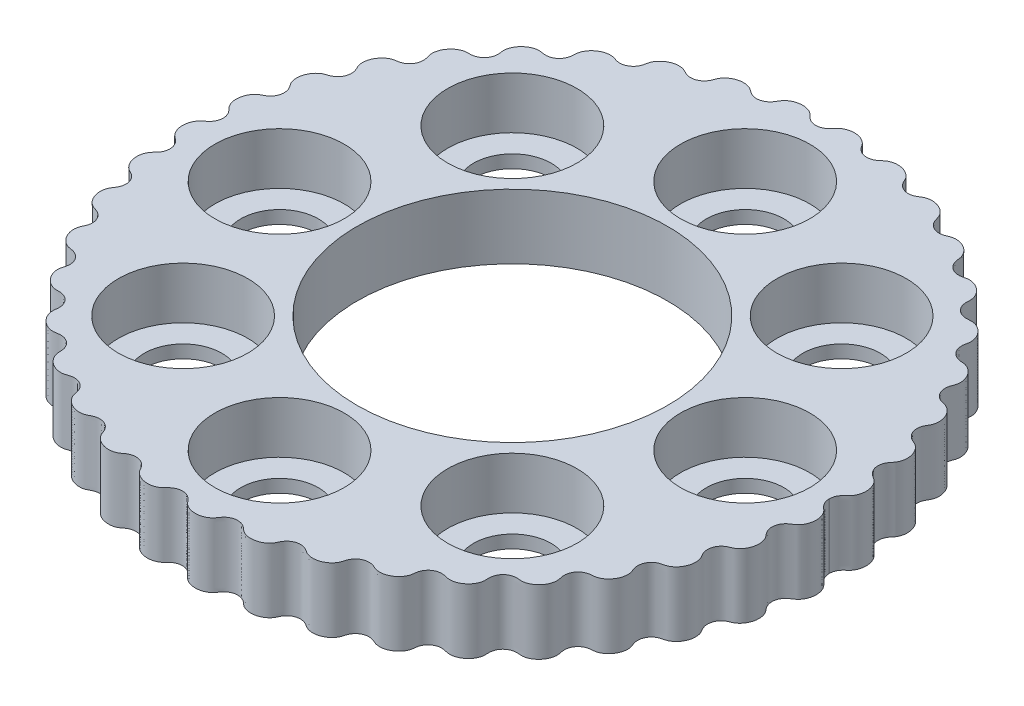
SolidWorks part; units mm, degrees
material "Plastic-FDM-PLA-pro"
ref_plane "Front Plane" through (0, 0, 0) normal (0, 0, 1) x (1, 0, 0)
ref_plane "Top Plane" through (0, 0, 0) normal (0, 1, 0) x (1, 0, 0)
ref_plane "Right Plane" through (0, 0, 0) normal (1, 0, 0) x (0, 0, -1)
sketch "Sketch1" plane through (0, 0, 0) normal (0, 1, 0) x (1, 0, 0)
  spline S0 degree 4 poles (21.6064, 11.6128) (21.6414, 11.4763) (21.7469, 11.2449) (21.9844, 10.9896) (22.3715, 10.8276) (22.6869, 10.7857) (22.9052, 10.6672) (23.101, 10.52) (23.2912, 10.3173) (23.4718, 10.0222) (23.5794, 9.667) (23.5943, 9.3186) (23.5416, 9.0412) (23.4555, 8.8423) (23.3486, 8.6778) (23.2672, 8.5195) (23.2069, 8.3378) (23.1769, 8.1351) (23.1918, 7.8658) (23.2852, 7.5991) (23.447, 7.374) (23.6777, 7.1845) (23.8829, 7.0851) (24.0858, 7.0142) (24.2547, 6.9048) (24.3764, 6.799) (24.5108, 6.6487) (24.6611, 6.4154) (24.7857, 6.0883) (24.8278, 5.7024) (24.7657, 5.333) (24.6291, 5.0248) (24.4255, 4.8149) (24.2352, 4.5318) (24.1366, 4.1601) (24.1814, 3.7967) (24.3419, 3.4935) (24.5162, 3.3067) (24.6648, 3.1936) (24.8483, 3.087) (25.0116, 2.971) (25.142, 2.817) (25.2689, 2.6137) (25.3735, 2.3636) (25.4403, 2.0313) (25.4214, 1.6748) (25.3264, 1.3624) (25.2002, 1.1354) (25.0791, 0.9924) (24.9144, 0.8484) (24.7545, 0.7145) (24.6219, 0.5035) (24.5339, 0.3154) (24.4987, 0.0763) (24.4972, -0.0467) (24.5201, -0.2316) (24.5633, -0.371) (24.6305, -0.5179) (24.7235, -0.6591) (24.8424, -0.7928) (24.9875, -0.9088) (25.1511, -1.0633) (25.293, -1.2851) (25.4049, -1.5905) (25.4424, -1.9737) (25.3882, -2.3415) (25.2499, -2.6627) (25.0662, -2.9239) (24.8433, -3.0978) (24.5517, -3.2517) (24.2918, -3.541) (24.1569, -3.8872) (24.16, -4.2453) (24.2535, -4.5391) (24.3852, -4.772) (24.6388, -5.0192) (24.7975, -5.3974) (24.8306, -5.8363) (24.735, -6.2498) (24.582, -6.5585) (24.3902, -6.792) (24.1849, -6.9706) (23.9409, -7.0651) (23.7071, -7.1659) (23.5087, -7.3191) (23.3504, -7.5023) (23.2169, -7.7647) (23.1632, -8.0717) (23.2057, -8.3939) (23.3413, -8.6751) (23.491, -8.8942) (23.5762, -9.1776) (23.5983, -9.4998) (23.5348, -9.8472) (23.3798, -10.1906) (23.1789, -10.451) (22.9676, -10.6305) (22.7649, -10.7428) (22.5892, -10.7977) (22.3868, -10.8377) (22.1901, -10.9044) (21.9966, -11.0169) (21.7651, -11.2346) (21.5956, -11.5351) (21.5394, -11.9062) (21.6321, -12.2847) (21.7646, -12.5496) (21.7896, -12.787) (21.7821, -13.0234) (21.7272, -13.2891) (21.5951, -13.6002) (21.3432, -13.9284) (21.0152, -14.1682) (20.6947, -14.2804) (20.4313, -14.2827) (20.2219, -14.3105) (20.0313, -14.3657) (19.7839, -14.4936) (19.5202, -14.7509) (19.3691, -15.1052) (19.358, -15.5014) (19.4626, -15.8335) (19.4645, -16.1376) (19.3797, -16.4671) (19.2041, -16.7975) (18.9497, -17.076) (18.6389, -17.2749) (18.3217, -17.3893) (18.0234, -17.406) (17.6885, -17.3481) (17.2876, -17.4221) (16.9111, -17.6604) (16.701, -18.015) (16.6406, -18.3304) (16.6445, -18.5921) (16.6666, -18.826) (16.6068, -19.103) (16.4483, -19.4313) (16.1768, -19.7449) (15.8266, -19.9759) (15.4618, -20.0854) (15.1639, -20.0942) (14.952, -20.0498) (14.7885, -20.002) (14.6205, -19.9753) (14.4515, -19.9734) (14.1835, -20.0112) (13.9066, -20.1364) (13.6633, -20.3656) (13.5183, -20.6583) (13.4634, -20.8736) (13.4458, -21.0651) (13.4259, -21.2273) (13.3666, -21.4185) (13.2572, -21.6273) (13.0672, -21.8645) (12.7739, -22.0937) (12.4479, -22.2382) (12.1139, -22.2969) (11.8439, -22.2832) (11.6455, -22.2339) (11.4786, -22.1566) (11.3266, -22.0917) (11.1442, -22.0428) (10.9328, -22.0228) (10.6452, -22.0575) (10.3631, -22.1865) (10.1408, -22.39) (9.9781, -22.6552) (9.9083, -22.8739) (9.8608, -23.0787) (9.7525, -23.2945) (9.5985, -23.4966) (9.3551, -23.7042) (9.0121, -23.8756) (8.6687, -23.9514) (8.3512, -23.9469) (8.1058, -23.89) (7.9336, -23.8157) (7.7931, -23.7235) (7.6679, -23.6413) (7.5165, -23.5662) (7.3372, -23.508) (7.0515, -23.4713) (6.6931, -23.5377) (6.3655, -23.7489) (6.1584, -24.0486) (6.0643, -24.2923) (5.9427, -24.495) (5.7771, -24.6722) (5.5202, -24.8548) (5.1577, -24.9945) (4.7865, -25.0373) (4.4327, -24.988) (4.1695, -24.8845) (3.9951, -24.7688) (3.8656, -24.6453) (3.7525, -24.5466) (3.6093, -24.4489) (3.4314, -24.3647) (3.1621, -24.2973) (2.8589, -24.3139) (2.5753, -24.4209) (2.3558, -24.59) (2.2246, -24.737) (2.1274, -24.882) (2.043, -25.0091) (1.9052, -25.1589) (1.6988, -25.3081) (1.3977, -25.4399) (1.0011, -25.503) (0.6294, -25.4653) (0.3077, -25.3467) (0.0836, -25.1987) (-0.0532, -25.0604) (-0.1778, -24.8926) (-0.3225, -24.7352) (-0.5188, -24.5957) (-0.7661, -24.4996) (-1.0146, -24.4675) (-1.2631, -24.4929) (-1.4934, -24.5761) (-1.7123, -24.7098) (-1.8904, -24.9013) (-2.0764, -25.0987) (-2.3287, -25.228) (-2.6322, -25.321) (-2.9953, -25.3415) (-3.3913, -25.2694) (-3.7257, -25.0998) (-3.9503, -24.901) (-4.079, -24.7143) (-4.1499, -24.578) (-4.2687, -24.3844) (-4.4849, -24.1551) (-4.8019, -23.9927) (-5.1889, -23.9616) (-5.4906, -24.0414) (-5.6943, -24.1469) (-5.8507, -24.2667) (-5.9811, -24.3697) (-6.1604, -24.4671) (-6.3907, -24.539) (-6.6975, -24.5713) (-7.0706, -24.5216) (-7.4033, -24.3887) (-7.679, -24.1911) (-7.8581, -23.9886) (-7.9629, -23.8127) (-8.0239, -23.6389) (-8.0813, -23.4835) (-8.1705, -23.3175) (-8.2998, -23.1506) (-8.5196, -22.9657) (-8.8045, -22.8475) (-9.1054, -22.8225) (-9.4112, -22.8846) (-9.6211, -22.9835) (-9.8015, -23.0932) (-10.0314, -23.1678) (-10.2833, -23.1991) (-10.6025, -23.1704) (-10.9638, -23.0446) (-11.2595, -22.8521) (-11.4763, -22.6216) (-11.6301, -22.3749) (-11.7084, -22.1238) (-11.7363, -21.8619) (-11.8445, -21.6178) (-12.0322, -21.3534) (-12.3288, -21.1371) (-12.7054, -21.043) (-13.067, -21.0972) (-13.3074, -21.197) (-13.5367, -21.2529) (-13.7784, -21.2587) (-14.0861, -21.2036) (-14.432, -21.0455) (-14.7219, -20.8162) (-14.9308, -20.5358) (-15.0653, -20.2461) (-15.1044, -19.966) (-15.092, -19.6366) (-15.2124, -19.2669) (-15.4448, -18.9769) (-15.7565, -18.8005) (-16.0577, -18.7346) (-16.3252, -18.7322) (-16.6661, -18.8282) (-17.073, -18.7766) (-17.4696, -18.5859) (-17.78, -18.2963) (-17.9708, -18.0094) (-18.0771, -17.7266) (-18.1291, -17.4595) (-18.089, -17.2009) (-18.0594, -16.9481) (-18.0928, -16.6996) (-18.1723, -16.471) (-18.3328, -16.2242) (-18.5719, -16.0241) (-18.8721, -15.8998) (-19.1835, -15.8766) (-19.4481, -15.8967) (-19.7361, -15.8288) (-20.0262, -15.6869) (-20.2953, -15.4582) (-20.5152, -15.1523) (-20.6403, -14.8481) (-20.6901, -14.5753) (-20.6859, -14.3436) (-20.6457, -14.164) (-20.5792, -13.9687) (-20.5386, -13.765) (-20.5392, -13.5412) (-20.612, -13.2319) (-20.7875, -12.9349) (-21.0807, -12.7006) (-21.4549, -12.5916) (-21.7505, -12.5739) (-21.9686, -12.4769) (-22.1696, -12.3522) (-22.3723, -12.1718) (-22.5756, -11.9018) (-22.7339, -11.5196) (-22.7776, -11.1156) (-22.7145, -10.782) (-22.5849, -10.5527) (-22.5042, -10.3575) (-22.4568, -10.1648) (-22.4437, -9.8866) (-22.5347, -9.5296) (-22.7659, -9.2216) (-23.1036, -9.0138) (-23.4433, -8.9385) (-23.708, -8.7878) (-23.9503, -8.5501) (-24.15, -8.2319) (-24.2617, -7.874) (-24.2819, -7.5029) (-24.2248, -7.2115) (-24.1394, -7.0047) (-24.0111, -6.8223) (-23.8576, -6.6068) (-23.7298, -6.2619) (-23.7513, -5.8143) (-23.9511, -5.4566) (-24.1952, -5.2457) (-24.4233, -5.1187) (-24.6372, -5.0206) (-24.847, -4.8305) (-25.0522, -4.5291) (-25.1879, -4.1371) (-25.213, -3.7183) (-25.1254, -3.3477) (-24.9841, -3.0853) (-24.8398, -2.924) (-24.7165, -2.8063) (-24.583, -2.6414) (-24.4354, -2.3636) (-24.3819, -2.0177) (-24.4687, -1.6501) (-24.6496, -1.3782) (-24.8086, -1.2229) (-24.9657, -1.1119) (-25.0962, -1.0135) (-25.2322, -0.8667) (-25.3584, -0.6675) (-25.4688, -0.3843) (-25.5206, -0.0157) (-25.4828, 0.3389) (-25.3667, 0.6575) (-25.2198, 0.8845) (-25.0779, 1.0317) (-24.9276, 1.1375) (-24.7953, 1.2367) (-24.6618, 1.3702) (-24.5388, 1.5433) (-24.4249, 1.8097) (-24.3956, 2.1184) (-24.4607, 2.4128) (-24.609, 2.6862) (-24.7635, 2.8561) (-24.9171, 2.9996) (-25.0499, 3.2013) (-25.1479, 3.4357) (-25.206, 3.7503) (-25.183, 4.133) (-25.0769, 4.4684) (-24.9143, 4.7411) (-24.7423, 4.9251) (-24.5919, 5.0371) (-24.4417, 5.1126) (-24.308, 5.18) (-24.1672, 5.2736) (-24.0272, 5.3998) (-23.8525, 5.6288) (-23.7308, 5.9724) (-23.7499, 6.3618) (-23.9059, 6.691) (-24.0699, 6.8943) (-24.1846, 7.1009) (-24.2553, 7.333) (-24.285, 7.6467) (-24.2247, 8.0305) (-24.0763, 8.3734) (-23.8566, 8.6551) (-23.6354, 8.8313) (-23.448, 8.9246) (-23.2763, 8.9749) (-23.1342, 9.0235) (-22.9781, 9.0987) (-22.8162, 9.2106) (-22.6231, 9.4101) (-22.486, 9.681) (-22.4368, 9.9801) (-22.4734, 10.2548) (-22.5351, 10.4418) (-22.6121, 10.5986) (-22.68, 10.7352) (-22.7408, 10.9295) (-22.7669, 11.1828) (-22.7304, 11.5095) (-22.5868, 11.8844) (-22.3683, 12.1876) (-22.1047, 12.4069) (-21.8645, 12.5269) (-21.6764, 12.5763) (-21.4687, 12.6003) (-21.2601, 12.6468) (-21.0411, 12.7471) (-20.8343, 12.9132) (-20.6822, 13.1123) (-20.5799, 13.3403) (-20.5369, 13.5813) (-20.5431, 13.8377) (-20.6199, 14.0877) (-20.6979, 14.3475) (-20.6838, 14.6306) (-20.6125, 14.94) (-20.4488, 15.2647) (-20.1883, 15.5716) (-19.8743, 15.7764) (-19.5899, 15.8715) (-19.3639, 15.8897) (-19.2104, 15.883) (-18.9834, 15.889) (-18.6767, 15.9615) (-18.3775, 16.1547) (-18.157, 16.4743) (-18.0752, 16.7755) (-18.0647, 17.0047) (-18.0902, 17.2001) (-18.1143, 17.3645) (-18.1089, 17.5685) (-18.0561, 17.8039) (-17.9307, 18.0858) (-17.7011, 18.3841) (-17.4196, 18.6058) (-17.1106, 18.7458) (-16.8457, 18.7996) (-16.641, 18.8024) (-16.46, 18.7684) (-16.2967, 18.7403) (-16.1084, 18.7346) (-15.8992, 18.7631) (-15.6291, 18.861) (-15.3843, 19.0486) (-15.2122, 19.2966) (-15.113, 19.5925) (-15.0937, 19.8238) (-15.0986, 20.035) (-15.0482, 20.2713) (-14.9494, 20.5052) (-14.765, 20.7672) (-14.4753, 21.0172) (-14.1608, 21.177) (-13.8528, 21.2496) (-13.5622, 21.2594) (-13.3057, 21.2017) (-13.0648, 21.0949) (-12.7994, 21.0666) (-12.4765, 21.0969) (-12.1409, 21.2456) (-11.8711, 21.5246) (-11.7372, 21.8649) (-11.7034, 22.123) (-11.6373, 22.3495) (-11.5214, 22.5617) (-11.3198, 22.8007) (-11.01, 23.0212) (-10.6664, 23.1577) (-10.3191, 23.1983) (-10.0011, 23.17) (-9.7389, 23.0639) (-9.4598, 22.8883) (-9.0794, 22.8078) (-8.7121, 22.864) (-8.4035, 23.0457) (-8.1958, 23.2737) (-8.06, 23.5041) (-7.9727, 23.8474) (-7.7246, 24.1739) (-7.3611, 24.4221) (-6.9551, 24.546) (-6.6113, 24.5678) (-6.3132, 24.5186) (-6.0559, 24.4301) (-5.8519, 24.266) (-5.6478, 24.114) (-5.4159, 24.0187) (-5.1781, 23.9732) (-4.8842, 23.9888) (-4.5914, 24.0957) (-4.3336, 24.2935) (-4.1578, 24.5516) (-4.043, 24.7909) (-3.8401, 25.0063) (-3.5722, 25.1866) (-3.2396, 25.3053) (-2.8647, 25.3428) (-2.5387, 25.299) (-2.2776, 25.2058) (-2.079, 25.0864) (-1.9435, 24.9618) (-1.8077, 24.8065) (-1.6516, 24.6695) (-1.4575, 24.5581) (-1.1533, 24.4665) (-0.8082, 24.4699) (-0.4587, 24.6067) (-0.1772, 24.8762) (-0.0141, 25.1234) (0.179, 25.2638) (0.3874, 25.3755) (0.645, 25.4608) (0.9805, 25.502) (1.3907, 25.448) (1.7624, 25.2838) (2.0197, 25.0624) (2.1535, 24.8355) (2.2823, 24.668) (2.4253, 24.5306) (2.6597, 24.3802) (3.0144, 24.2805) (3.3968, 24.3266) (3.7456, 24.5152) (3.9807, 24.7717) (4.2435, 24.9256) (4.5705, 25.0166) (4.9458, 25.0305) (5.3119, 24.9483) (5.643, 24.7801) (5.8673, 24.5852) (6.0028, 24.4076) (6.0826, 24.2396) (6.143, 24.1028) (6.2565, 23.9062) (6.4759, 23.6637) (6.8407, 23.4765) (7.2497, 23.4705) (7.5547, 23.5765) (7.7786, 23.7105) (7.9706, 23.8467) (8.2401, 23.9334) (8.6038, 23.9604) (9.011, 23.882) (9.3863, 23.6943) (9.6634, 23.4332) (9.82, 23.1796) (9.8876, 22.974) (9.9279, 22.8084) (10.0039, 22.6103) (10.1706, 22.3437) (10.4434, 22.1243) (10.8051, 22.0156) (11.1311, 22.0362) (11.3451, 22.0963) (11.5198, 22.1769) (11.6703, 22.2407) (11.8654, 22.285) (12.101, 22.2948) (12.4015, 22.2488) (12.7467, 22.1094) (13.0348, 21.8994) (13.2527, 21.6395) (13.3758, 21.3988) (13.4324, 21.2023) (13.4489, 21.0192) (13.4686, 20.855) (13.5175, 20.6726) (13.6059, 20.4796) (13.7797, 20.2478) (14.0324, 20.068) (14.3198, 19.9772) (14.6308, 19.9689) (14.8552, 20.0177) (15.0562, 20.079) (15.2973, 20.0932) (15.5493, 20.0609) (15.8508, 19.9539) (16.1707, 19.7426) (16.4081, 19.4831) (16.563, 19.2059) (16.6364, 18.9649) (16.6582, 18.7787) (16.6486, 18.6109) (16.64, 18.4614) (16.6507, 18.2926) (16.6899, 18.1083) (16.8009, 17.8425) (17.0376, 17.5653) (17.3843, 17.3871) (17.7475, 17.3576) (18.0055, 17.398) (18.2418, 17.394) (18.4781, 17.3393) (18.7647, 17.2081) (19.0669, 16.964) (19.2897, 16.664) (19.4239, 16.3329) (19.4658, 16.0532) (19.4529, 15.8443) (19.4107, 15.6704) (19.3817, 15.5231) (19.3687, 15.3503) (19.3847, 15.1541) (19.4609, 14.8872) (19.6269, 14.633) (19.8614, 14.4408) (20.1176, 14.3352) (20.3104, 14.2951) (20.4846, 14.2834) (20.6369, 14.2739) (20.8355, 14.2294) (21.068, 14.1253) (21.3326, 13.9304) (21.5856, 13.6186) (21.7389, 13.2778) (21.797, 12.9399) (21.7809, 12.6717) (21.7296, 12.4842) (21.6466, 12.2922) (21.5826, 12.0887) (21.5598, 11.8481) (21.6099, 11.5263) (21.753, 11.2421) (21.9754, 11.0236) (22.2554, 10.8726) (22.5102, 10.8132) (22.7742, 10.7514) (23.0124, 10.5973) (23.2447, 10.3811) (23.444, 10.0768) (23.5796, 9.6979) (23.5999, 9.3235) (23.5401, 9.0297) (23.4429, 8.8249) (23.3603, 8.6953) (23.252, 8.4958) (23.1614, 8.1939) (23.1791, 7.8382) (23.3456, 7.4874) (23.5655, 7.2659) (23.7587, 7.1422) (23.9407, 7.0666) (24.0951, 7.0052) (24.2692, 6.8986) (24.4466, 6.7352) (24.6287, 6.4847) (24.7728, 6.1345) (24.8235, 5.7774) (24.7881, 5.4376) (24.7001, 5.1799) (24.5973, 5.0011) (24.4749, 4.8604) (24.3681, 4.7299) (24.27, 4.5656) (24.1928, 4.366) (24.1487, 4.0806) (24.1956, 3.7768) (24.3283, 3.5111) (24.5371, 3.2801) (24.7311, 3.1513) (24.9205, 3.0449) (25.0679, 2.9033) (25.172, 2.7726) (25.2819, 2.5886) (25.3847, 2.3274) (25.4421, 1.9891) (25.4127, 1.6245) (25.3025, 1.3024) (25.1554, 1.0688) (25.0038, 0.9249) (24.8611, 0.8033) (24.7491, 0.6995) (24.6413, 0.5276) (24.5505, 0.3764) (24.4955, 0.0867) (24.4947, -0.0797) (24.5547, -0.3974) (24.6786, -0.5985) (24.8655, -0.8322) (25.1022, -0.9903) (25.2927, -1.2763) (25.4173, -1.6256) (25.4428, -2.0161) (25.3682, -2.397) (25.2352, -2.6864) (25.0928, -2.88) (24.9184, -3.0461) (24.7326, -3.1512) (24.5436, -3.2751) (24.3796, -3.4542) (24.2658, -3.6365) (24.168, -3.906) (24.1508, -4.2123) (24.2348, -4.5312) (24.4248, -4.814) (24.6285, -5.0241) (24.7655, -5.332) (24.8277, -5.7016) (24.786, -6.0872) (24.6469, -6.4527) (24.4651, -6.7144) (24.2897, -6.8818) (24.0868, -7.0138) (23.8842, -7.0847) (23.6788, -7.1838) (23.448, -7.3729) (23.2859, -7.5977) (23.1922, -7.8642) (23.1769, -8.1335) (23.2066, -8.3362) (23.2665, -8.518) (23.3478, -8.6765) (23.4547, -8.8409) (23.5411, -9.0397) (23.5942, -9.3169) (23.5797, -9.6657) (23.4731, -10.0182) (23.274, -10.3468) (23.052, -10.568) (22.8501, -10.7012) (22.6276, -10.7926) (22.4169, -10.8278) (22.2005, -10.8982) (21.9459, -11.0512) (21.7636, -11.2408) (21.6636, -11.4244) (21.6175, -11.5694) (21.6065, -11.6122) knots 0 0 0 0 0 0.002654 0.004786 0.006316 0.007845 0.008629 0.009413 0.01098 0.013063 0.015147 0.016343 0.017539 0.018381 0.019222 0.020064 0.020905 0.021995 0.023085 0.025147 0.026164 0.027182 0.028699 0.029457 0.030216 0.030982 0.031748 0.033281 0.035433 0.037585 0.038965 0.040346 0.041714 0.043082 0.0454 0.04745 0.048461 0.049472 0.050225 0.050979 0.052487 0.053248 0.054009 0.055531 0.057585 0.059638 0.060666 0.061695 0.062456 0.063216 0.064738 0.065778 0.066818 0.067667 0.068385 0.069102 0.06982 0.070538 0.071421 0.072304 0.073187 0.07407 0.075664 0.077258 0.079288 0.081318 0.082594 0.083869 0.085257 0.086645 0.088819 0.091044 0.092148 0.093252 0.094656 0.096059 0.098784 0.100818 0.102852 0.104037 0.105222 0.106567 0.107911 0.108976 0.110041 0.111265 0.11249 0.114477 0.115881 0.117284 0.118381 0.119479 0.121426 0.123373 0.124976 0.126579 0.127595 0.12861 0.129335 0.13006 0.131509 0.132527 0.133545 0.136038 0.137928 0.13939 0.140852 0.141613 0.142374 0.143896 0.145943 0.147989 0.150092 0.151522 0.152237 0.152953 0.154104 0.155255 0.157496 0.159774 0.16119 0.162605 0.16404 0.165474 0.167569 0.169664 0.171057 0.172449 0.173868 0.175287 0.177453 0.179996 0.182057 0.182779 0.183501 0.184946 0.186499 0.188052 0.190377 0.192702 0.194343 0.195163 0.195983 0.196782 0.19758 0.198378 0.199176 0.201896 0.203215 0.204534 0.205309 0.206084 0.206859 0.207634 0.209084 0.210533 0.21258 0.214627 0.215764 0.216902 0.217685 0.218468 0.219251 0.220035 0.221253 0.222471 0.224698 0.225787 0.226877 0.228317 0.229037 0.229758 0.231433 0.233109 0.235038 0.236967 0.238024 0.239082 0.239792 0.240502 0.241211 0.241921 0.242991 0.24406 0.246641 0.248667 0.250125 0.250854 0.251582 0.253135 0.254688 0.25678 0.258872 0.260133 0.261393 0.262104 0.262815 0.263526 0.264237 0.265383 0.26653 0.268747 0.269884 0.271022 0.271745 0.272469 0.273192 0.273915 0.27559 0.277265 0.279359 0.281454 0.28258 0.283706 0.284416 0.285125 0.286544 0.287742 0.288939 0.290102 0.291266 0.292418 0.29357 0.294896 0.296222 0.297533 0.298845 0.300929 0.303013 0.305103 0.305832 0.306561 0.307291 0.30802 0.310135 0.312462 0.313832 0.315203 0.315991 0.316778 0.317566 0.318354 0.31984 0.321326 0.323373 0.32542 0.326557 0.327694 0.328479 0.329264 0.330049 0.330835 0.33204 0.333245 0.335451 0.33656 0.33767 0.339111 0.339831 0.340552 0.342227 0.343903 0.345831 0.34776 0.348819 0.349878 0.351296 0.352714 0.353787 0.354859 0.357437 0.359474 0.360925 0.36165 0.362375 0.363928 0.365481 0.367512 0.369542 0.370817 0.372093 0.373481 0.374869 0.377042 0.379268 0.380372 0.381476 0.382879 0.384283 0.387008 0.389042 0.391076 0.392261 0.393446 0.39479 0.396135 0.3972 0.398265 0.399489 0.400713 0.402701 0.404104 0.405508 0.406605 0.407703 0.409649 0.411596 0.4132 0.414803 0.415818 0.416834 0.417559 0.418283 0.419732 0.42075 0.421768 0.424262 0.426152 0.427613 0.429075 0.429836 0.430598 0.43212 0.434166 0.436213 0.438316 0.439746 0.440461 0.441176 0.442327 0.443479 0.44572 0.447998 0.449413 0.450829 0.452263 0.453698 0.455793 0.457888 0.459281 0.460673 0.461383 0.462092 0.463511 0.465677 0.46822 0.47028 0.471003 0.471725 0.47317 0.474723 0.476276 0.478601 0.480926 0.482566 0.483386 0.484207 0.485005 0.485803 0.487399 0.490119 0.491438 0.492758 0.493533 0.494308 0.495082 0.495857 0.497307 0.498757 0.500804 0.50285 0.503988 0.505125 0.505909 0.506692 0.507475 0.508258 0.509476 0.510695 0.512921 0.514011 0.515101 0.516541 0.517261 0.517981 0.519657 0.521333 0.523262 0.52519 0.526248 0.527306 0.528016 0.528725 0.529435 0.530145 0.531214 0.532283 0.534865 0.536891 0.538348 0.539077 0.539806 0.541359 0.542912 0.545004 0.547096 0.548356 0.549617 0.550328 0.551039 0.55175 0.55246 0.553607 0.554754 0.556971 0.558108 0.559246 0.559969 0.560692 0.561416 0.562139 0.563814 0.565488 0.567583 0.569678 0.570804 0.57193 0.572639 0.573349 0.574768 0.575965 0.577163 0.578326 0.579489 0.580642 0.581794 0.58312 0.584446 0.585757 0.587068 0.589152 0.591236 0.593326 0.594055 0.594785 0.595514 0.596243 0.598358 0.600685 0.602055 0.603426 0.604214 0.605002 0.605789 0.606577 0.608064 0.60955 0.611597 0.613643 0.61478 0.615918 0.616703 0.617488 0.618273 0.619058 0.620264 0.621469 0.623674 0.624784 0.625893 0.627335 0.628055 0.628776 0.630451 0.632126 0.634055 0.635984 0.637043 0.638101 0.63952 0.640938 0.64201 0.643082 0.645661 0.647698 0.649148 0.649874 0.650599 0.652152 0.653705 0.655735 0.657765 0.659041 0.660317 0.661705 0.663093 0.665266 0.667492 0.668596 0.669699 0.671103 0.672507 0.675231 0.677266 0.6793 0.680485 0.68167 0.683014 0.684359 0.685424 0.686489 0.687713 0.688937 0.690925 0.692328 0.693731 0.694829 0.695926 0.697873 0.69982 0.701423 0.703027 0.704042 0.705058 0.705782 0.706507 0.707956 0.708974 0.709992 0.712486 0.714375 0.715837 0.717299 0.71806 0.718821 0.720343 0.72239 0.724437 0.72654 0.72797 0.728685 0.7294 0.730551 0.731702 0.733943 0.736221 0.737637 0.739053 0.740487 0.741921 0.744017 0.746112 0.747504 0.748897 0.749606 0.750316 0.751025 0.751735 0.753901 0.756444 0.758504 0.759227 0.759949 0.761394 0.762947 0.7645 0.766824 0.769149 0.77079 0.77161 0.77243 0.773228 0.774026 0.775622 0.778342 0.779661 0.780981 0.781756 0.782531 0.783306 0.784081 0.785531 0.786981 0.789028 0.791074 0.792212 0.793349 0.794132 0.794916 0.795699 0.796482 0.7977 0.798918 0.801145 0.802235 0.803324 0.804765 0.805485 0.806205 0.807881 0.809556 0.811485 0.813414 0.814472 0.81553 0.816239 0.816949 0.817659 0.818369 0.819438 0.820507 0.823088 0.825114 0.826572 0.827301 0.82803 0.829583 0.831135 0.833228 0.83532 0.83658 0.83784 0.838551 0.839262 0.839973 0.840684 0.841831 0.842977 0.845194 0.846332 0.847469 0.848193 0.848916 0.849639 0.850363 0.852037 0.853712 0.855807 0.857901 0.859027 0.860153 0.860863 0.861572 0.862991 0.864189 0.865387 0.867713 0.868865 0.870018 0.871344 0.872669 0.873981 0.875292 0.877376 0.87946 0.881549 0.882279 0.883008 0.883737 0.884467 0.88658 0.888908 0.890278 0.891649 0.892437 0.893225 0.894013 0.894801 0.896287 0.897774 0.899841 0.901908 0.903047 0.904185 0.904984 0.905783 0.906582 0.907381 0.908599 0.909817 0.912014 0.913081 0.914148 0.915663 0.91642 0.917177 0.918002 0.918827 0.920477 0.922466 0.924455 0.925669 0.926883 0.927647 0.928411 0.929175 0.929939 0.931136 0.932332 0.933492 0.934652 0.936022 0.937392 0.938775 0.940157 0.942313 0.944468 0.94599 0.947512 0.948266 0.949019 0.950527 0.951537 0.952548 0.953572 0.954597 0.956916 0.958284 0.959652 0.961032 0.962413 0.964565 0.966717 0.968249 0.969781 0.97054 0.971298 0.972814 0.973831 0.974848 0.976909 0.977999 0.979089 0.979931 0.980772 0.981614 0.982456 0.983652 0.984848 0.986931 0.989015 0.990541 0.992067 0.992821 0.993575 0.995082 0.996098 0.997114 0.999166 1 1 1 1 1 construction
  spline S1 degree 4 poles (24.5, 0) (24.5, -0.0327) (24.5036, -0.0989) (24.5201, -0.2316) (24.5633, -0.371) (24.6305, -0.5179) (24.7235, -0.6591) (24.8424, -0.7928) (24.9875, -0.9088) (25.1511, -1.0633) (25.293, -1.2851) (25.4049, -1.5905) (25.4424, -1.9737) (25.3882, -2.3415) (25.2499, -2.6627) (25.0662, -2.9239) (24.8433, -3.0978) (24.5517, -3.2517) (24.2918, -3.541) (24.1569, -3.8872) (24.16, -4.2453) (24.2535, -4.5391) (24.3852, -4.772) (24.6388, -5.0192) (24.7975, -5.3974) (24.8306, -5.8363) (24.735, -6.2498) (24.582, -6.5585) (24.3902, -6.792) (24.1849, -6.9706) (23.9409, -7.0651) (23.7071, -7.1659) (23.5087, -7.3191) (23.3504, -7.5023) (23.2169, -7.7647) (23.1632, -8.0717) (23.2057, -8.3939) (23.3413, -8.6751) (23.491, -8.8942) (23.5762, -9.1776) (23.5983, -9.4998) (23.5348, -9.8472) (23.3798, -10.1906) (23.1789, -10.451) (22.9676, -10.6305) (22.7649, -10.7428) (22.5892, -10.7977) (22.3868, -10.8377) (22.1901, -10.9044) (21.9966, -11.0169) (21.7651, -11.2346) (21.5956, -11.5351) (21.5394, -11.9062) (21.6321, -12.2847) (21.7646, -12.5496) (21.7896, -12.787) (21.7821, -13.0234) (21.7272, -13.2891) (21.5951, -13.6002) (21.3432, -13.9284) (21.0152, -14.1682) (20.6947, -14.2804) (20.4313, -14.2827) (20.2219, -14.3105) (20.0313, -14.3657) (19.7839, -14.4936) (19.5202, -14.7509) (19.3691, -15.1052) (19.358, -15.5014) (19.4626, -15.8335) (19.4645, -16.1376) (19.3797, -16.4671) (19.2041, -16.7975) (18.9497, -17.076) (18.6389, -17.2749) (18.3217, -17.3893) (18.0234, -17.406) (17.6885, -17.3481) (17.2876, -17.4221) (16.9111, -17.6604) (16.701, -18.015) (16.6406, -18.3304) (16.6445, -18.5921) (16.6666, -18.826) (16.6068, -19.103) (16.4483, -19.4313) (16.1768, -19.7449) (15.8266, -19.9759) (15.4618, -20.0854) (15.1639, -20.0942) (14.952, -20.0498) (14.7885, -20.002) (14.6205, -19.9753) (14.4515, -19.9734) (14.1835, -20.0112) (13.9066, -20.1364) (13.6633, -20.3656) (13.5183, -20.6583) (13.4634, -20.8736) (13.4458, -21.0651) (13.4259, -21.2273) (13.3666, -21.4185) (13.2572, -21.6273) (13.0672, -21.8645) (12.7739, -22.0937) (12.4479, -22.2382) (12.1139, -22.2969) (11.8439, -22.2832) (11.6455, -22.2339) (11.4786, -22.1566) (11.3266, -22.0917) (11.1442, -22.0428) (10.9328, -22.0228) (10.6452, -22.0575) (10.3631, -22.1865) (10.1408, -22.39) (9.9781, -22.6552) (9.9083, -22.8739) (9.8608, -23.0787) (9.7525, -23.2945) (9.5985, -23.4966) (9.3551, -23.7042) (9.0121, -23.8756) (8.6687, -23.9514) (8.3512, -23.9469) (8.1058, -23.89) (7.9336, -23.8157) (7.7931, -23.7235) (7.6679, -23.6413) (7.5165, -23.5662) (7.3372, -23.508) (7.0515, -23.4713) (6.6931, -23.5377) (6.3655, -23.7489) (6.1584, -24.0486) (6.0643, -24.2923) (5.9427, -24.495) (5.7771, -24.6722) (5.5202, -24.8548) (5.1577, -24.9945) (4.7865, -25.0373) (4.4327, -24.988) (4.1695, -24.8845) (3.9951, -24.7688) (3.8656, -24.6453) (3.7525, -24.5466) (3.6093, -24.4489) (3.4314, -24.3647) (3.1621, -24.2973) (2.8589, -24.3139) (2.5753, -24.4209) (2.3558, -24.59) (2.2246, -24.737) (2.1274, -24.882) (2.043, -25.0091) (1.9052, -25.1589) (1.6988, -25.3081) (1.3977, -25.4399) (1.0011, -25.503) (0.6294, -25.4653) (0.3077, -25.3467) (0.0836, -25.1987) (-0.0532, -25.0604) (-0.1778, -24.8926) (-0.3225, -24.7352) (-0.5188, -24.5957) (-0.7661, -24.4996) (-1.0146, -24.4675) (-1.2631, -24.4929) (-1.4934, -24.5761) (-1.7123, -24.7098) (-1.8904, -24.9013) (-2.0764, -25.0987) (-2.3287, -25.228) (-2.6322, -25.321) (-2.9953, -25.3415) (-3.3913, -25.2694) (-3.7257, -25.0998) (-3.9503, -24.901) (-4.079, -24.7143) (-4.1499, -24.578) (-4.2687, -24.3844) (-4.4849, -24.1551) (-4.8019, -23.9927) (-5.1889, -23.9616) (-5.4906, -24.0414) (-5.6943, -24.1469) (-5.8507, -24.2667) (-5.9811, -24.3697) (-6.1604, -24.4671) (-6.3907, -24.539) (-6.6975, -24.5713) (-7.0706, -24.5216) (-7.4033, -24.3887) (-7.679, -24.1911) (-7.8581, -23.9886) (-7.9629, -23.8127) (-8.0239, -23.6389) (-8.0813, -23.4835) (-8.1705, -23.3175) (-8.2998, -23.1506) (-8.5196, -22.9657) (-8.8045, -22.8475) (-9.1054, -22.8225) (-9.4112, -22.8846) (-9.6211, -22.9835) (-9.8015, -23.0932) (-10.0314, -23.1678) (-10.2833, -23.1991) (-10.6025, -23.1704) (-10.9638, -23.0446) (-11.2595, -22.8521) (-11.4763, -22.6216) (-11.6301, -22.3749) (-11.7084, -22.1238) (-11.7363, -21.8619) (-11.8445, -21.6178) (-12.0322, -21.3534) (-12.3288, -21.1371) (-12.7054, -21.043) (-13.067, -21.0972) (-13.3074, -21.197) (-13.5367, -21.2529) (-13.7784, -21.2587) (-14.0861, -21.2036) (-14.432, -21.0455) (-14.7219, -20.8162) (-14.9308, -20.5358) (-15.0653, -20.2461) (-15.1044, -19.966) (-15.092, -19.6366) (-15.2124, -19.2669) (-15.4448, -18.9769) (-15.7565, -18.8005) (-16.0577, -18.7346) (-16.3252, -18.7322) (-16.6661, -18.8282) (-17.073, -18.7766) (-17.4696, -18.5859) (-17.78, -18.2963) (-17.9708, -18.0094) (-18.0771, -17.7266) (-18.1291, -17.4595) (-18.089, -17.2009) (-18.0594, -16.9481) (-18.0928, -16.6996) (-18.1723, -16.471) (-18.3328, -16.2242) (-18.5719, -16.0241) (-18.8721, -15.8998) (-19.1835, -15.8766) (-19.4481, -15.8967) (-19.7361, -15.8288) (-20.0262, -15.6869) (-20.2953, -15.4582) (-20.5152, -15.1523) (-20.6403, -14.8481) (-20.6901, -14.5753) (-20.6859, -14.3436) (-20.6457, -14.164) (-20.5792, -13.9687) (-20.5386, -13.765) (-20.5392, -13.5412) (-20.612, -13.2319) (-20.7875, -12.9349) (-21.0807, -12.7006) (-21.4549, -12.5916) (-21.7505, -12.5739) (-21.9686, -12.4769) (-22.1696, -12.3522) (-22.3723, -12.1718) (-22.5756, -11.9018) (-22.7339, -11.5196) (-22.7776, -11.1156) (-22.7145, -10.782) (-22.5849, -10.5527) (-22.5042, -10.3575) (-22.4568, -10.1648) (-22.4437, -9.8866) (-22.5347, -9.5296) (-22.7659, -9.2216) (-23.1036, -9.0138) (-23.4433, -8.9385) (-23.708, -8.7878) (-23.9503, -8.5501) (-24.15, -8.2319) (-24.2617, -7.874) (-24.2819, -7.5029) (-24.2248, -7.2115) (-24.1394, -7.0047) (-24.0111, -6.8223) (-23.8576, -6.6068) (-23.7298, -6.2619) (-23.7513, -5.8143) (-23.9511, -5.4566) (-24.1952, -5.2457) (-24.4233, -5.1187) (-24.6372, -5.0206) (-24.847, -4.8305) (-25.0522, -4.5291) (-25.1879, -4.1371) (-25.213, -3.7183) (-25.1254, -3.3477) (-24.9841, -3.0853) (-24.8398, -2.924) (-24.7165, -2.8063) (-24.583, -2.6414) (-24.4354, -2.3636) (-24.3819, -2.0177) (-24.4687, -1.6501) (-24.6496, -1.3782) (-24.8086, -1.2229) (-24.9657, -1.1119) (-25.0962, -1.0135) (-25.2322, -0.8667) (-25.3584, -0.6675) (-25.4688, -0.3843) (-25.5206, -0.0157) (-25.4828, 0.3389) (-25.3667, 0.6575) (-25.2198, 0.8845) (-25.0779, 1.0317) (-24.9276, 1.1375) (-24.7953, 1.2367) (-24.6618, 1.3702) (-24.5388, 1.5433) (-24.4249, 1.8097) (-24.3956, 2.1184) (-24.4607, 2.4128) (-24.609, 2.6862) (-24.7635, 2.8561) (-24.9171, 2.9996) (-25.0499, 3.2013) (-25.1479, 3.4357) (-25.206, 3.7503) (-25.183, 4.133) (-25.0769, 4.4684) (-24.9143, 4.7411) (-24.7423, 4.9251) (-24.5919, 5.0371) (-24.4417, 5.1126) (-24.308, 5.18) (-24.1672, 5.2736) (-24.0272, 5.3998) (-23.8525, 5.6288) (-23.7308, 5.9724) (-23.7499, 6.3618) (-23.9059, 6.691) (-24.0699, 6.8943) (-24.1846, 7.1009) (-24.2553, 7.333) (-24.285, 7.6467) (-24.2247, 8.0305) (-24.0763, 8.3734) (-23.8566, 8.6551) (-23.6354, 8.8313) (-23.448, 8.9246) (-23.2763, 8.9749) (-23.1342, 9.0235) (-22.9781, 9.0987) (-22.8162, 9.2106) (-22.6231, 9.4101) (-22.486, 9.681) (-22.4368, 9.9801) (-22.4734, 10.2548) (-22.5351, 10.4418) (-22.6121, 10.5986) (-22.68, 10.7352) (-22.7408, 10.9295) (-22.7669, 11.1828) (-22.7304, 11.5095) (-22.5868, 11.8844) (-22.3683, 12.1876) (-22.1047, 12.4069) (-21.8645, 12.5269) (-21.6764, 12.5763) (-21.4687, 12.6003) (-21.2601, 12.6468) (-21.0411, 12.7471) (-20.8343, 12.9132) (-20.6822, 13.1123) (-20.5799, 13.3403) (-20.5369, 13.5813) (-20.5431, 13.8377) (-20.6199, 14.0877) (-20.6979, 14.3475) (-20.6838, 14.6306) (-20.6125, 14.94) (-20.4488, 15.2647) (-20.1883, 15.5716) (-19.8743, 15.7764) (-19.5899, 15.8715) (-19.3639, 15.8897) (-19.2104, 15.883) (-18.9834, 15.889) (-18.6767, 15.9615) (-18.3775, 16.1547) (-18.157, 16.4743) (-18.0752, 16.7755) (-18.0647, 17.0047) (-18.0902, 17.2001) (-18.1143, 17.3645) (-18.1089, 17.5685) (-18.0561, 17.8039) (-17.9307, 18.0858) (-17.7011, 18.3841) (-17.4196, 18.6058) (-17.1106, 18.7458) (-16.8457, 18.7996) (-16.641, 18.8024) (-16.46, 18.7684) (-16.2967, 18.7403) (-16.1084, 18.7346) (-15.8992, 18.7631) (-15.6291, 18.861) (-15.3843, 19.0486) (-15.2122, 19.2966) (-15.113, 19.5925) (-15.0937, 19.8238) (-15.0986, 20.035) (-15.0482, 20.2713) (-14.9494, 20.5052) (-14.765, 20.7672) (-14.4753, 21.0172) (-14.1608, 21.177) (-13.8528, 21.2496) (-13.5622, 21.2594) (-13.3057, 21.2017) (-13.0648, 21.0949) (-12.7994, 21.0666) (-12.4765, 21.0969) (-12.1409, 21.2456) (-11.8711, 21.5246) (-11.7372, 21.8649) (-11.7034, 22.123) (-11.6373, 22.3495) (-11.5214, 22.5617) (-11.3198, 22.8007) (-11.01, 23.0212) (-10.6664, 23.1577) (-10.3191, 23.1983) (-10.0011, 23.17) (-9.7389, 23.0639) (-9.4598, 22.8883) (-9.0794, 22.8078) (-8.7121, 22.864) (-8.4035, 23.0457) (-8.1958, 23.2737) (-8.06, 23.5041) (-7.9727, 23.8474) (-7.7246, 24.1739) (-7.3611, 24.4221) (-6.9551, 24.546) (-6.6113, 24.5678) (-6.3132, 24.5186) (-6.0559, 24.4301) (-5.8519, 24.266) (-5.6478, 24.114) (-5.4159, 24.0187) (-5.1781, 23.9732) (-4.8842, 23.9888) (-4.5914, 24.0957) (-4.3336, 24.2935) (-4.1578, 24.5516) (-4.043, 24.7909) (-3.8401, 25.0063) (-3.5722, 25.1866) (-3.2396, 25.3053) (-2.8647, 25.3428) (-2.5387, 25.299) (-2.2776, 25.2058) (-2.079, 25.0864) (-1.9435, 24.9618) (-1.8077, 24.8065) (-1.6516, 24.6695) (-1.4575, 24.5581) (-1.1533, 24.4665) (-0.8082, 24.4699) (-0.4587, 24.6067) (-0.1772, 24.8762) (-0.0141, 25.1234) (0.179, 25.2638) (0.3874, 25.3755) (0.645, 25.4608) (0.9805, 25.502) (1.3907, 25.448) (1.7624, 25.2838) (2.0197, 25.0624) (2.1535, 24.8355) (2.2823, 24.668) (2.4253, 24.5306) (2.6597, 24.3802) (3.0144, 24.2805) (3.3968, 24.3266) (3.7456, 24.5152) (3.9807, 24.7717) (4.2435, 24.9256) (4.5705, 25.0166) (4.9458, 25.0305) (5.3119, 24.9483) (5.643, 24.7801) (5.8673, 24.5852) (6.0028, 24.4076) (6.0826, 24.2396) (6.143, 24.1028) (6.2565, 23.9062) (6.4759, 23.6637) (6.8407, 23.4765) (7.2497, 23.4705) (7.5547, 23.5765) (7.7786, 23.7105) (7.9706, 23.8467) (8.2401, 23.9334) (8.6038, 23.9604) (9.011, 23.882) (9.3863, 23.6943) (9.6634, 23.4332) (9.82, 23.1796) (9.8876, 22.974) (9.9279, 22.8084) (10.0039, 22.6103) (10.1706, 22.3437) (10.4434, 22.1243) (10.8051, 22.0156) (11.1311, 22.0362) (11.3451, 22.0963) (11.5198, 22.1769) (11.6703, 22.2407) (11.8654, 22.285) (12.101, 22.2948) (12.4015, 22.2488) (12.7467, 22.1094) (13.0348, 21.8994) (13.2527, 21.6395) (13.3758, 21.3988) (13.4324, 21.2023) (13.4489, 21.0192) (13.4686, 20.855) (13.5175, 20.6726) (13.6059, 20.4796) (13.7797, 20.2478) (14.0324, 20.068) (14.3198, 19.9772) (14.6308, 19.9689) (14.8552, 20.0177) (15.0562, 20.079) (15.2973, 20.0932) (15.5493, 20.0609) (15.8508, 19.9539) (16.1707, 19.7426) (16.4081, 19.4831) (16.563, 19.2059) (16.6364, 18.9649) (16.6582, 18.7787) (16.6486, 18.6109) (16.64, 18.4614) (16.6507, 18.2926) (16.6899, 18.1083) (16.8009, 17.8425) (17.0376, 17.5653) (17.3843, 17.3871) (17.7475, 17.3576) (18.0055, 17.398) (18.2418, 17.394) (18.4781, 17.3393) (18.7647, 17.2081) (19.0669, 16.964) (19.2897, 16.664) (19.4239, 16.3329) (19.4658, 16.0532) (19.4529, 15.8443) (19.4107, 15.6704) (19.3817, 15.5231) (19.3687, 15.3503) (19.3847, 15.1541) (19.4609, 14.8872) (19.6269, 14.633) (19.8614, 14.4408) (20.1176, 14.3352) (20.3104, 14.2951) (20.4846, 14.2834) (20.6369, 14.2739) (20.8355, 14.2294) (21.068, 14.1253) (21.3326, 13.9304) (21.5856, 13.6186) (21.7389, 13.2778) (21.797, 12.9399) (21.7809, 12.6717) (21.7296, 12.4842) (21.6466, 12.2922) (21.5826, 12.0887) (21.5598, 11.8481) (21.6099, 11.5263) (21.753, 11.2421) (21.9754, 11.0236) (22.2554, 10.8726) (22.5102, 10.8132) (22.7742, 10.7514) (23.0124, 10.5973) (23.2447, 10.3811) (23.444, 10.0768) (23.5796, 9.6979) (23.5999, 9.3235) (23.5401, 9.0297) (23.4429, 8.8249) (23.3603, 8.6953) (23.252, 8.4958) (23.1614, 8.1939) (23.1791, 7.8382) (23.3456, 7.4874) (23.5655, 7.2659) (23.7587, 7.1422) (23.9407, 7.0666) (24.0951, 7.0052) (24.2692, 6.8986) (24.4466, 6.7352) (24.6287, 6.4847) (24.7728, 6.1345) (24.8235, 5.7774) (24.7881, 5.4376) (24.7001, 5.1799) (24.5973, 5.0011) (24.4749, 4.8604) (24.3681, 4.7299) (24.27, 4.5656) (24.1928, 4.366) (24.1487, 4.0806) (24.1956, 3.7768) (24.3283, 3.5111) (24.5371, 3.2801) (24.7311, 3.1513) (24.9205, 3.0449) (25.0679, 2.9033) (25.172, 2.7726) (25.2819, 2.5886) (25.3847, 2.3274) (25.4421, 1.9891) (25.4127, 1.6245) (25.3025, 1.3024) (25.1554, 1.0688) (25.0038, 0.9249) (24.8611, 0.8033) (24.7491, 0.6995) (24.6413, 0.5276) (24.5505, 0.3764) (24.5102, 0.1646) (24.5, 0.0552) (24.5, 0.0007) knots 0.067667 0.067667 0.067667 0.067667 0.067667 0.068385 0.069102 0.06982 0.070538 0.071421 0.072304 0.073187 0.07407 0.075664 0.077258 0.079288 0.081318 0.082594 0.083869 0.085257 0.086645 0.088819 0.091044 0.092148 0.093252 0.094656 0.096059 0.098784 0.100818 0.102852 0.104037 0.105222 0.106567 0.107911 0.108976 0.110041 0.111265 0.11249 0.114477 0.115881 0.117284 0.118381 0.119479 0.121426 0.123373 0.124976 0.126579 0.127595 0.12861 0.129335 0.13006 0.131509 0.132527 0.133545 0.136038 0.137928 0.13939 0.140852 0.141613 0.142374 0.143896 0.145943 0.147989 0.150092 0.151522 0.152237 0.152953 0.154104 0.155255 0.157496 0.159774 0.16119 0.162605 0.16404 0.165474 0.167569 0.169664 0.171057 0.172449 0.173868 0.175287 0.177453 0.179996 0.182057 0.182779 0.183501 0.184946 0.186499 0.188052 0.190377 0.192702 0.194343 0.195163 0.195983 0.196782 0.19758 0.198378 0.199176 0.201896 0.203215 0.204534 0.205309 0.206084 0.206859 0.207634 0.209084 0.210533 0.21258 0.214627 0.215764 0.216902 0.217685 0.218468 0.219251 0.220035 0.221253 0.222471 0.224698 0.225787 0.226877 0.228317 0.229037 0.229758 0.231433 0.233109 0.235038 0.236967 0.238024 0.239082 0.239792 0.240502 0.241211 0.241921 0.242991 0.24406 0.246641 0.248667 0.250125 0.250854 0.251582 0.253135 0.254688 0.25678 0.258872 0.260133 0.261393 0.262104 0.262815 0.263526 0.264237 0.265383 0.26653 0.268747 0.269884 0.271022 0.271745 0.272469 0.273192 0.273915 0.27559 0.277265 0.279359 0.281454 0.28258 0.283706 0.284416 0.285125 0.286544 0.287742 0.288939 0.290102 0.291266 0.292418 0.29357 0.294896 0.296222 0.297533 0.298845 0.300929 0.303013 0.305103 0.305832 0.306561 0.307291 0.30802 0.310135 0.312462 0.313832 0.315203 0.315991 0.316778 0.317566 0.318354 0.31984 0.321326 0.323373 0.32542 0.326557 0.327694 0.328479 0.329264 0.330049 0.330835 0.33204 0.333245 0.335451 0.33656 0.33767 0.339111 0.339831 0.340552 0.342227 0.343903 0.345831 0.34776 0.348819 0.349878 0.351296 0.352714 0.353787 0.354859 0.357437 0.359474 0.360925 0.36165 0.362375 0.363928 0.365481 0.367512 0.369542 0.370817 0.372093 0.373481 0.374869 0.377042 0.379268 0.380372 0.381476 0.382879 0.384283 0.387008 0.389042 0.391076 0.392261 0.393446 0.39479 0.396135 0.3972 0.398265 0.399489 0.400713 0.402701 0.404104 0.405508 0.406605 0.407703 0.409649 0.411596 0.4132 0.414803 0.415818 0.416834 0.417559 0.418283 0.419732 0.42075 0.421768 0.424262 0.426152 0.427613 0.429075 0.429836 0.430598 0.43212 0.434166 0.436213 0.438316 0.439746 0.440461 0.441176 0.442327 0.443479 0.44572 0.447998 0.449413 0.450829 0.452263 0.453698 0.455793 0.457888 0.459281 0.460673 0.461383 0.462092 0.463511 0.465677 0.46822 0.47028 0.471003 0.471725 0.47317 0.474723 0.476276 0.478601 0.480926 0.482566 0.483386 0.484207 0.485005 0.485803 0.487399 0.490119 0.491438 0.492758 0.493533 0.494308 0.495082 0.495857 0.497307 0.498757 0.500804 0.50285 0.503988 0.505125 0.505909 0.506692 0.507475 0.508258 0.509476 0.510695 0.512921 0.514011 0.515101 0.516541 0.517261 0.517981 0.519657 0.521333 0.523262 0.52519 0.526248 0.527306 0.528016 0.528725 0.529435 0.530145 0.531214 0.532283 0.534865 0.536891 0.538348 0.539077 0.539806 0.541359 0.542912 0.545004 0.547096 0.548356 0.549617 0.550328 0.551039 0.55175 0.55246 0.553607 0.554754 0.556971 0.558108 0.559246 0.559969 0.560692 0.561416 0.562139 0.563814 0.565488 0.567583 0.569678 0.570804 0.57193 0.572639 0.573349 0.574768 0.575965 0.577163 0.578326 0.579489 0.580642 0.581794 0.58312 0.584446 0.585757 0.587068 0.589152 0.591236 0.593326 0.594055 0.594785 0.595514 0.596243 0.598358 0.600685 0.602055 0.603426 0.604214 0.605002 0.605789 0.606577 0.608064 0.60955 0.611597 0.613643 0.61478 0.615918 0.616703 0.617488 0.618273 0.619058 0.620264 0.621469 0.623674 0.624784 0.625893 0.627335 0.628055 0.628776 0.630451 0.632126 0.634055 0.635984 0.637043 0.638101 0.63952 0.640938 0.64201 0.643082 0.645661 0.647698 0.649148 0.649874 0.650599 0.652152 0.653705 0.655735 0.657765 0.659041 0.660317 0.661705 0.663093 0.665266 0.667492 0.668596 0.669699 0.671103 0.672507 0.675231 0.677266 0.6793 0.680485 0.68167 0.683014 0.684359 0.685424 0.686489 0.687713 0.688937 0.690925 0.692328 0.693731 0.694829 0.695926 0.697873 0.69982 0.701423 0.703027 0.704042 0.705058 0.705782 0.706507 0.707956 0.708974 0.709992 0.712486 0.714375 0.715837 0.717299 0.71806 0.718821 0.720343 0.72239 0.724437 0.72654 0.72797 0.728685 0.7294 0.730551 0.731702 0.733943 0.736221 0.737637 0.739053 0.740487 0.741921 0.744017 0.746112 0.747504 0.748897 0.749606 0.750316 0.751025 0.751735 0.753901 0.756444 0.758504 0.759227 0.759949 0.761394 0.762947 0.7645 0.766824 0.769149 0.77079 0.77161 0.77243 0.773228 0.774026 0.775622 0.778342 0.779661 0.780981 0.781756 0.782531 0.783306 0.784081 0.785531 0.786981 0.789028 0.791074 0.792212 0.793349 0.794132 0.794916 0.795699 0.796482 0.7977 0.798918 0.801145 0.802235 0.803324 0.804765 0.805485 0.806205 0.807881 0.809556 0.811485 0.813414 0.814472 0.81553 0.816239 0.816949 0.817659 0.818369 0.819438 0.820507 0.823088 0.825114 0.826572 0.827301 0.82803 0.829583 0.831135 0.833228 0.83532 0.83658 0.83784 0.838551 0.839262 0.839973 0.840684 0.841831 0.842977 0.845194 0.846332 0.847469 0.848193 0.848916 0.849639 0.850363 0.852037 0.853712 0.855807 0.857901 0.859027 0.860153 0.860863 0.861572 0.862991 0.864189 0.865387 0.867713 0.868865 0.870018 0.871344 0.872669 0.873981 0.875292 0.877376 0.87946 0.881549 0.882279 0.883008 0.883737 0.884467 0.88658 0.888908 0.890278 0.891649 0.892437 0.893225 0.894013 0.894801 0.896287 0.897774 0.899841 0.901908 0.903047 0.904185 0.904984 0.905783 0.906582 0.907381 0.908599 0.909817 0.912014 0.913081 0.914148 0.915663 0.91642 0.917177 0.918002 0.918827 0.920477 0.922466 0.924455 0.925669 0.926883 0.927647 0.928411 0.929175 0.929939 0.931136 0.932332 0.932332 0.932332 0.932332 0.932332
  spline S2 degree 1 poles (24.5, 0.0007) (24.5, 0) knots 0 0 1 1
extrude "Boss-Extrude1" add sketch "Sketch1" along normal blind 5 contours S1 S2
sketch "Sketch2" plane through (0, 5, 0) normal (0, 1, 0) x (1, 0, 0)
  circle A0 centre (0, 0) radius 12
  point P22 (0, 0)
  dimension "D1" = 24
extrude "Cut-Extrude1" cut sketch "Sketch2" against normal through all
sketch "Sketch4" plane through (0, 5, 0) normal (0, 1, 0) x (1, 0, 0)
  point P0 (18, 0)
  point P4 (12.7279, -12.7279)
  point P6 (0, -18)
  point P7 (-12.7279, -12.7279)
  point P8 (-18, 0)
  point P9 (-12.7279, 12.7279)
  point P10 (0, 18)
  point P11 (12.7279, 12.7279)
  dimension "D1" = 8
hole_wizard "Hole1" positions "Sketch4" profile "Sketch7" legacy
sketch "Sketch7" plane through (18, 5, 0) normal (1, 0, 0) x (0, 0, 1)
  line L0 (0, 0) -> (0, 5)
  line L1 (0, 5) -> (3, 5)
  line L2 (3, 5) -> (3, 4)
  line L3 (3, 4) -> (5, 4)
  line L4 (5, 4) -> (5, 0)
  line L5 (5, 0) -> (0, 0)
  line L6 (0, 110) -> (0, -10) construction
  dimension "Diameter" = 6
  dimension "Depth" = 5
  dimension "C-Bore Diameter" = 10
  dimension "C-Bore Depth" = 4
equation "\"R\"= 26mm'Radius of the rollers PCD (Pitch Circle Diamater)"
equation "\"Rr\"= 1mm'Radius of the roller"
equation "\"Z\"= 4mm'Number of rollers"
equation "\"E\"= 0.5'Eccentricity"
equation "\"shaftEBOD\"= 24mm"
equation "\"pinBOD\" = 9mm"
equation "\"pinBW\"= 4mm"
equation "\"shaftEBW\"= 5mm"
equation "\"Dt\"= \"shaftEBW\""
equation "\"pinpitchdia\"= 18mm"
